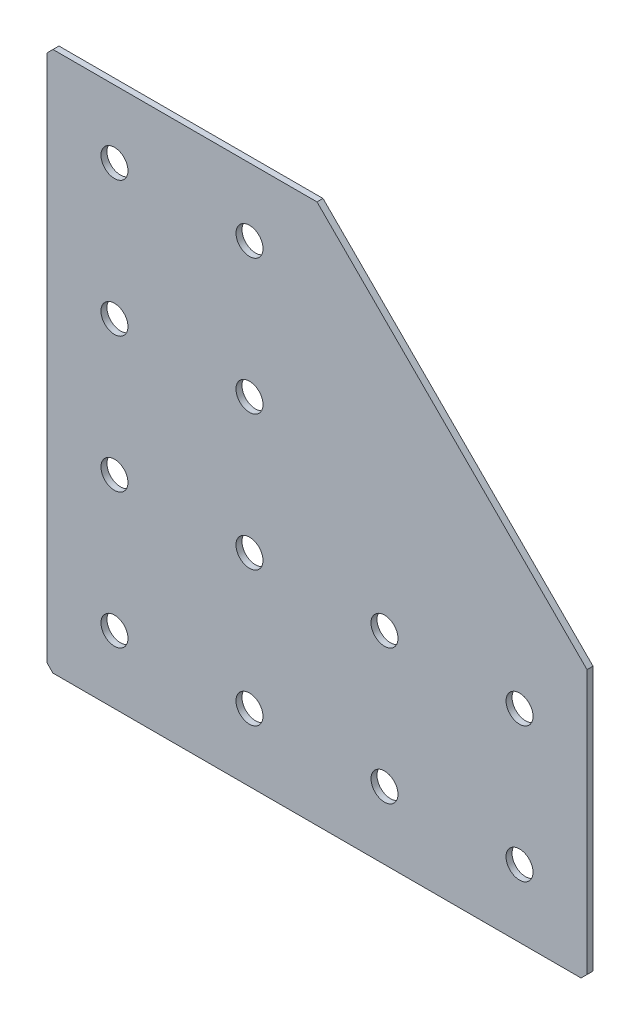
SolidWorks part; units mm, degrees
material "Простая углеродистая сталь"
ref_plane "Спереди(Плоскость XY)" through (0, 0, 0) normal (0, 0, 1) x (1, 0, 0)
ref_plane "Сверху(Плоскость XZ)" through (0, 0, 0) normal (0, 1, 0) x (1, 0, 0)
ref_plane "Справа(Плоскость ZY)" through (0, 0, 0) normal (1, 0, 0) x (0, 0, -1)
sketch "Эскиз1" plane through (0, 0, 0) normal (0, 0, -1) x (1, 0, 0)
  line L0 (0, 0) -> (0, 180)
  line L1 (0, 180) -> (180, 180)
  line L2 (180, 180) -> (180, 90)
  line L3 (180, 90) -> (90, 90) construction
  line L4 (90, 90) -> (90, 0) construction
  line L5 (90, 0) -> (0, 0)
  line L6 (180, 90) -> (90, 0)
  dimension "D1" = 180
  dimension "D2" = 90
  dimension "D3" = 90
  dimension "D4" = 180
extrude "Бобышка-Вытянуть1" add sketch "Эскиз1" along normal blind 2
hole_wizard "Отверстие с зазором M81" positions "Эскиз2" profile "Эскиз3" hole size "M8" standard "DIN" end condition through all
sketch "Эскиз2" plane through (0, 0, -2) normal (0, 0, -1) x (1, 0, 0)
  line L0 (22.5, 0) -> (22.5, 180) construction
  line L1 (0, 0) -> (90, 0) construction
  line L2 (180, 180) -> (0, 180) construction
  line L3 (0, 180) -> (0, 0) construction
  line L4 (0, 0) -> (90, 0) construction
  point P0 (22.5, 157.5)
  point P2 (22.5, 112.5)
  point P4 (22.5, 67.5)
  point P6 (22.5, 22.5)
  point P27 (67.5, 157.5)
  point P29 (67.5, 112.5)
  point P35 (67.5, 67.5)
  point P37 (67.5, 22.5)
  point P39 (112.5, 157.5)
  point P41 (112.5, 112.5)
  point P53 (157.5, 157.5)
  point P55 (157.5, 112.5)
  dimension "D1" = 45
  dimension "D2" = 45
  dimension "D3" = 45
  dimension "D4" = 22.5
  dimension "D5" = 45
  dimension "D6" = 22.5
  dimension "D7" = 45
  dimension "D8" = 45
sketch "Эскиз3" plane through (22.5, -157.5, -2) normal (1, 0, 0) x (0, 1, 0)
  line L0 (0, 0) -> (0, 2)
  line L1 (0, 2) -> (4.5, 2)
  line L2 (4.5, 2) -> (4.5, 0)
  line L5 (4.5, 0) -> (0, 0)
  line L11 (0, -6.35) -> (0, 107.95) construction
  dimension "Диаметр сквозного отверстия" = 9
  dimension "Глубина сквозного отверстия" = 2
chamfer "Фаска1" distance 2 angle 45 3 edges at (0, 0, -1) (180, -180, -1) (0, -180, -1)
